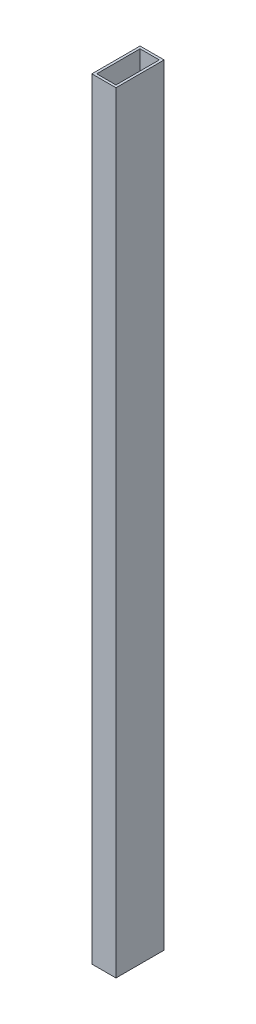
SolidWorks part; units mm, degrees
ref_plane "Спереди" through (0, 0, 0) normal (0, 0, 1) x (1, 0, 0)
ref_plane "Сверху" through (0, 0, 0) normal (0, 1, 0) x (1, 0, 0)
ref_plane "Справа" through (0, 0, 0) normal (1, 0, 0) x (0, 0, -1)
sketch "Sketch1" plane through (0, 0, 0) normal (0, 1, 0) x (1, 0, 0)
  line L1 (5, -10) -> (-5, -10)
  line L2 (5, -10) -> (5, 10)
  line L3 (5, 10) -> (-5, 10)
  line L4 (-5, -10) -> (-5, 10)
  line L5 (5, -10) -> (-5, 10) construction
  line L6 (5, 10) -> (-5, -10) construction
  line L7 (4, -9) -> (-4, -9)
  line L8 (4, -9) -> (4, 9)
  line L9 (4, 9) -> (-4, 9)
  line L10 (-4, -9) -> (-4, 9)
  line L11 (4, -9) -> (-4, 9) construction
  line L12 (4, 9) -> (-4, -9) construction
  point P0 (0, 0)
  point P6 (0, 0)
  dimension "D1" = 10
  dimension "D2" = 20
  dimension "D3" = 1
  dimension "D4" = 1
extrude "Boss-Extrude1" add sketch "Sketch1" along normal blind 320
